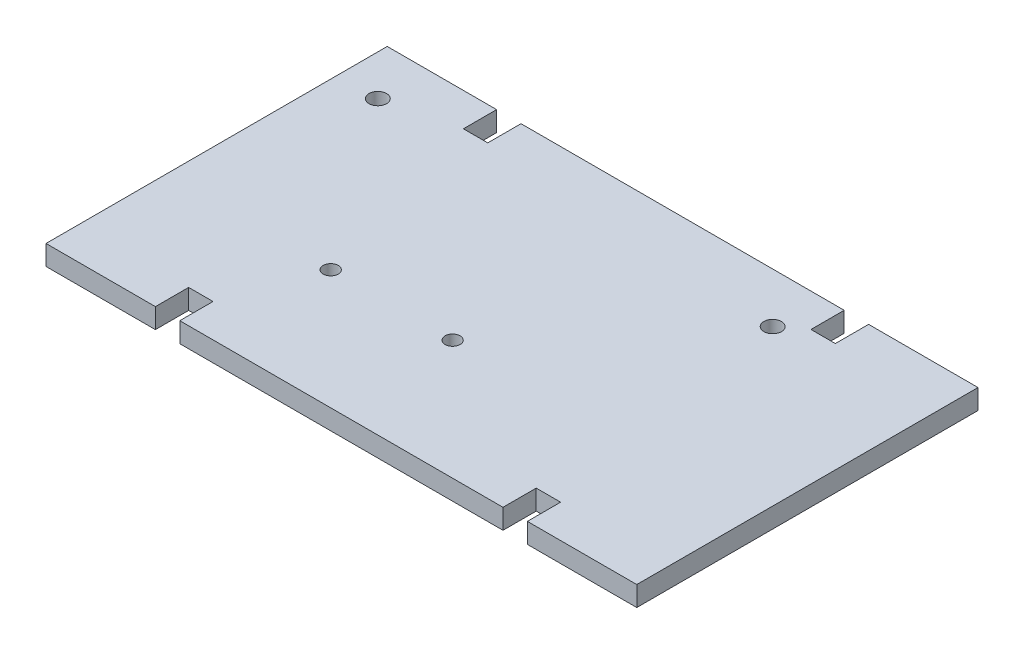
SolidWorks part; units mm, degrees
ref_plane "Front Plane" through (0, 0, 0) normal (0, 0, 1) x (1, 0, 0)
ref_plane "Top Plane" through (0, 0, 0) normal (0, 1, 0) x (1, 0, 0)
ref_plane "Right Plane" through (0, 0, 0) normal (1, 0, 0) x (0, 0, -1)
sketch "Sketch1" plane through (0, 0, 0) normal (0, 1, 0) x (1, 0, 0)
  line L0 (-42.6212, 39.1) -> (-37.0332, 39.1) construction
  line L1 (-67.691, 31.48) -> (67.691, 31.48)
  line L2 (-67.691, 31.48) -> (-67.691, -31.48)
  line L3 (-67.691, -31.48) -> (67.691, -31.48)
  line L4 (67.691, 31.48) -> (67.691, -31.48)
  line L5 (-67.691, 31.48) -> (67.691, -31.48) construction
  line L6 (-67.691, -31.48) -> (67.691, 31.48) construction
  line L7 (-67.691, 31.48) -> (-42.6212, 31.48)
  line L8 (-67.691, 31.48) -> (-67.691, 39.1)
  line L9 (-67.691, 39.1) -> (-42.6212, 39.1)
  line L10 (-42.6212, 31.48) -> (-42.6212, 39.1)
  line L11 (-37.0332, 31.48) -> (37.0332, 31.48)
  line L12 (-37.0332, 31.48) -> (-37.0332, 39.1)
  line L13 (-37.0332, 39.1) -> (37.0332, 39.1)
  line L14 (37.0332, 31.48) -> (37.0332, 39.1)
  line L15 (67.691, 31.48) -> (42.6212, 31.48)
  line L16 (67.691, 31.48) -> (67.691, 39.1)
  line L17 (67.691, 39.1) -> (42.6212, 39.1)
  line L18 (42.6212, 31.48) -> (42.6212, 39.1)
  line L19 (37.0332, 39.1) -> (42.6212, 39.1) construction
  line L20 (-67.691, 0) -> (67.691, 0) construction
  line L21 (37.0332, -39.1) -> (42.6212, -39.1) construction
  line L22 (-42.6212, -39.1) -> (-37.0332, -39.1) construction
  line L23 (42.6212, -31.48) -> (42.6212, -39.1)
  line L24 (67.691, -39.1) -> (42.6212, -39.1)
  line L25 (67.691, -31.48) -> (67.691, -39.1)
  line L26 (67.691, -31.48) -> (42.6212, -31.48)
  line L27 (37.0332, -31.48) -> (37.0332, -39.1)
  line L28 (-37.0332, -39.1) -> (37.0332, -39.1)
  line L29 (-37.0332, -31.48) -> (-37.0332, -39.1)
  line L30 (-37.0332, -31.48) -> (37.0332, -31.48)
  line L31 (-42.6212, -31.48) -> (-42.6212, -39.1)
  line L32 (-67.691, -39.1) -> (-42.6212, -39.1)
  line L33 (-67.691, -31.48) -> (-67.691, -39.1)
  line L34 (-67.691, -31.48) -> (-42.6212, -31.48)
  point P0 (0, 0)
  point P16 (-39.8272, 39.1)
  point P17 (39.8272, 39.1)
  dimension "D1" = 135.382
  dimension "D2" = 62.96
  dimension "D3" = 79.6544
  dimension "D4" = 5.588
  dimension "D5" = 7.62
extrude "Boss-Extrude1" add sketch "Sketch1" along normal blind 4.572 contours L4 L1 L2 L3 | L18 L1 L16 L17 | L1 L14 L13 L12 | L1 L10 L9 L8 | L3 L33 L32 L31 | L3 L29 L28 L27 | L25 L3 L23 L24
hole_wizard "#10-32 Tapped Hole1" positions "Sketch3" profile "Sketch4" tap size "#10-32" standard "ANSI Inch" end condition through all
sketch "Sketch3" plane through (0, 4.572, 0) normal (0, 1, 0) x (1, 0, 0)
  line L4 (-67.691, 39.1) -> (-42.6212, 39.1) construction
  line L5 (-67.691, 39.1) -> (-67.691, -39.1) construction
  point P0 (-58.42, 27.67)
  point P2 (32.0675, 27.67)
  point P17 (0, 0)
  point P20 (-52.0823, 39.1)
  point P25 (-67.691, 15.5796)
  point P28 (-67.691, 4.5262)
  dimension "D1" = 11.43
  dimension "D2" = 9.271
  dimension "D3" = 90.4875
sketch "Sketch4" plane through (-58.42, 4.572, -27.67) normal (1, 0, 0) x (0, 0, 1)
  line L0 (0, 0) -> (0, 4.572)
  line L1 (0, 4.572) -> (2.0193, 4.572)
  line L2 (2.0193, 4.572) -> (2.0193, 0)
  line L5 (2.0193, 0) -> (0, 0)
  line L11 (0, -6.35) -> (0, 107.95) construction
  dimension "Thru Tap Drill Dia." = 4.0386
  dimension "Thru Tap Drill Depth" = 4.572
cosmetic thread "Hole Thread1" parameters "D1"=4.572, "D2"=4.826
cosmetic thread "Hole Thread2" parameters "D1"=4.572, "D2"=4.826
hole_wizard "#8-32 Tapped Hole1" positions "Sketch5" profile "Sketch6" tap size "#8-32" standard "ANSI Inch" end condition through all
sketch "Sketch5" plane through (0, 4.572, 0) normal (0, 1, 0) x (1, 0, 0)
  line L2 (-37.0332, -39.1) -> (37.0332, -39.1) construction
  line L3 (-67.691, 39.1) -> (-67.691, -39.1) construction
  point P0 (-29.845, -11.7)
  point P2 (-1.905, -11.7)
  point P11 (18.4909, -39.1)
  point P18 (-67.691, -13.7459)
  point P21 (-67.691, -17.1854)
  dimension "D1" = 27.94
  dimension "D2" = 27.4
  dimension "D3" = 37.846
sketch "Sketch6" plane through (-29.845, 4.572, 11.7) normal (1, 0, 0) x (0, 0, 1)
  line L0 (0, 0) -> (0, 4.572)
  line L1 (0, 4.572) -> (1.7272, 4.572)
  line L2 (1.7272, 4.572) -> (1.7272, 0)
  line L5 (1.7272, 0) -> (0, 0)
  line L11 (0, -6.35) -> (0, 107.95) construction
  dimension "Thru Tap Drill Dia." = 3.4544
  dimension "Thru Tap Drill Depth" = 4.572
cosmetic thread "Hole Thread3" parameters "D1"=4.572, "D2"=4.1656
cosmetic thread "Hole Thread4" parameters "D1"=4.572, "D2"=4.1656
